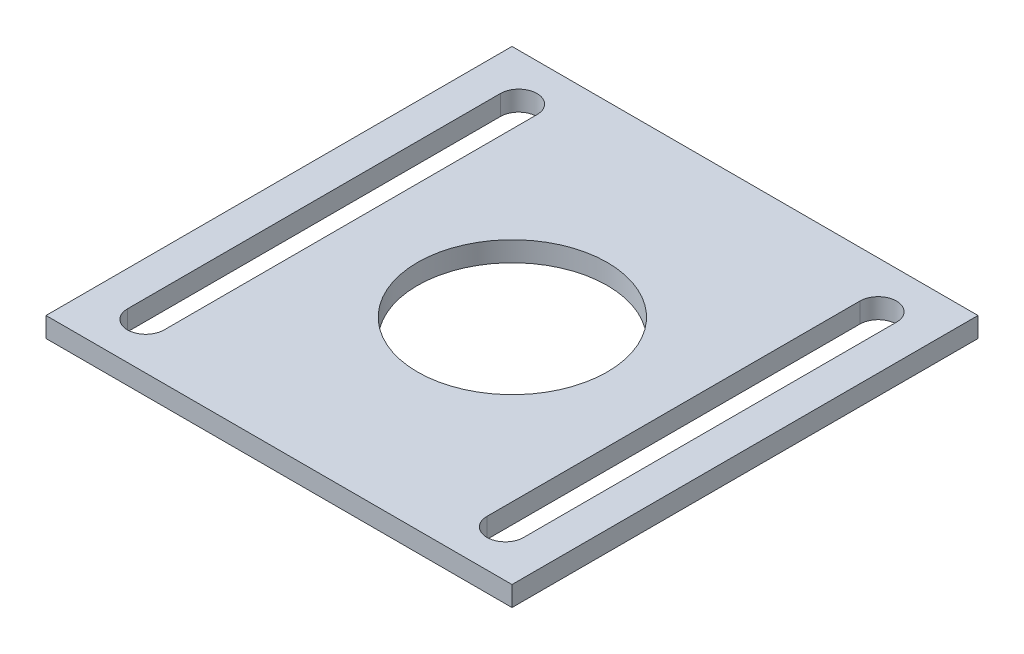
SolidWorks part; units mm, degrees
ref_plane "Front Plane" through (0, 0, 0) normal (0, 0, 1) x (1, 0, 0)
ref_plane "Top Plane" through (0, 0, 0) normal (0, 1, 0) x (1, 0, 0)
ref_plane "Right Plane" through (0, 0, 0) normal (1, 0, 0) x (0, 0, -1)
sketch "Sketch1" plane through (0, 0, 0) normal (0, 1, 0) x (1, 0, 0)
  line L1 (0, 0) -> (70, 0)
  line L2 (0, 0) -> (0, 70)
  line L3 (0, 70) -> (70, 70)
  line L4 (70, 0) -> (70, 70)
  dimension "D1" = 70
  dimension "7" = 70
extrude "Boss-Extrude1" add sketch "Sketch1" along normal blind 3 contours L3 L4 L1 L2
sketch "Sketch2" plane through (0, 3, 0) normal (0, 1, 0) x (1, 0, 0)
  line L0 (8, 63.0084) -> (8, 6.9916) construction
  line L1 (10.75, 63.0084) -> (10.75, 6.9916)
  line L2 (5.25, 63.0084) -> (5.25, 6.9916)
  line L3 (62, 63.0084) -> (62, 6.9916) construction
  line L4 (64.75, 63.0084) -> (64.75, 6.9916)
  line L5 (59.25, 63.0084) -> (59.25, 6.9916)
  line L7 (0, 35) -> (70, 35) construction
  line L8 (0, 0) -> (0, 70) construction
  line L9 (70, 0) -> (70, 70) construction
  circle A0 centre (35.2514, 34.8026) radius 14.255
  arc A1 (10.75, 63.0084) -> (5.25, 63.0084) centre (8, 63.0084) ccw
  arc A2 (5.25, 6.9916) -> (10.75, 6.9916) centre (8, 6.9916) ccw
  arc A3 (64.75, 63.0084) -> (59.25, 63.0084) centre (62, 63.0084) ccw
  arc A4 (59.25, 6.9916) -> (64.75, 6.9916) centre (62, 6.9916) ccw
  point P4 (8, 35)
  point P9 (62, 35)
  dimension "D1" = 28.51
  dimension "D2" = 5.5
  dimension "D3" = 5.5
  dimension "D4" = 8
  dimension "D5" = 8
extrude "Cut-Extrude1" cut sketch "Sketch2" against normal blind 3
